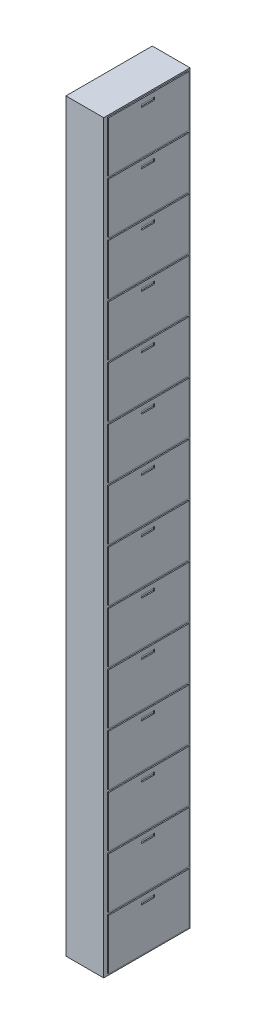
SolidWorks part; units mm, degrees
ref_plane "Front Plane" through (0, 0, 0) normal (0, 0, 1) x (1, 0, 0)
ref_plane "Top Plane" through (0, 0, 0) normal (0, 1, 0) x (1, 0, 0)
ref_plane "Right Plane" through (0, 0, 0) normal (1, 0, 0) x (0, 0, -1)
sketch "Sketch1" plane through (0, 0, 0) normal (0, 0, 1) x (1, 0, 0)
  line L0 (213.062, 4179.9863) -> (-136.938, 4179.9863)
  line L1 (-136.938, 4179.9863) -> (-136.938, -2720.0137)
  line L2 (-136.938, -2720.0137) -> (213.062, -2720.0137)
  line L5 (213.062, -2720.0137) -> (213.062, 4179.9863)
  dimension "D1" = 350
  dimension "D2" = 6900
extrude "Boss-Extrude1" add sketch "Sketch1" along normal blind 800
sketch "Sketch3" plane through (213.062, 0, 0) normal (1, 0, 0) x (0, 0, -1)
  line L0 (0, -2720.0137) -> (0, 4179.9863) construction
  line L1 (-763.6321, -2700.0137) -> (-20, -2700.0137)
  line L2 (-763.6321, -2700.0137) -> (-763.6321, -2230.0137)
  line L3 (-763.6321, -2230.0137) -> (-20, -2230.0137)
  line L4 (-20, -2700.0137) -> (-20, -2230.0137)
  line L5 (-800, -2720.0137) -> (0, -2720.0137) construction
  line L6 (-763.6321, -2208.0137) -> (-20, -2208.0137)
  line L7 (-461.6648, -2274.1108) -> (-340.5919, -2274.1108)
  line L8 (-461.6648, -2274.1108) -> (-461.6648, -2299.9132)
  line L9 (-461.6648, -2299.9132) -> (-340.5919, -2299.9132)
  line L10 (-340.5919, -2274.1108) -> (-340.5919, -2299.9132)
  line L11 (-763.6321, -2208.0137) -> (-763.6321, -1738.0137)
  line L12 (-763.6321, -1738.0137) -> (-20, -1738.0137)
  line L13 (-20, -2208.0137) -> (-20, -1738.0137)
  line L14 (-461.6648, -1782.1108) -> (-340.5919, -1782.1108)
  line L15 (-461.6648, -1807.9132) -> (-340.5919, -1807.9132)
  line L16 (-461.6648, -1782.1108) -> (-461.6648, -1807.9132)
  line L17 (-340.5919, -1782.1108) -> (-340.5919, -1807.9132)
  line L18 (-763.6321, -1716.0137) -> (-20, -1716.0137)
  line L19 (-763.6321, -1716.0137) -> (-763.6321, -1246.0137)
  line L20 (-763.6321, -1246.0137) -> (-20, -1246.0137)
  line L21 (-20, -1716.0137) -> (-20, -1246.0137)
  line L22 (-461.6648, -1290.1108) -> (-340.5919, -1290.1108)
  line L23 (-461.6648, -1315.9132) -> (-340.5919, -1315.9132)
  line L24 (-461.6648, -1290.1108) -> (-461.6648, -1315.9132)
  line L25 (-340.5919, -1290.1108) -> (-340.5919, -1315.9132)
  line L26 (-763.6321, -1224.0137) -> (-20, -1224.0137)
  line L27 (-763.6321, -1224.0137) -> (-763.6321, -754.0137)
  line L28 (-763.6321, -754.0137) -> (-20, -754.0137)
  line L29 (-20, -1224.0137) -> (-20, -754.0137)
  line L30 (-461.6648, -798.1108) -> (-340.5919, -798.1108)
  line L31 (-461.6648, -823.9132) -> (-340.5919, -823.9132)
  line L34 (-461.6648, -798.1108) -> (-461.6648, -823.9132)
  line L35 (-340.5919, -798.1108) -> (-340.5919, -823.9132)
  line L36 (-763.6321, -732.0137) -> (-20, -732.0137)
  line L37 (-763.6321, -732.0137) -> (-763.6321, -262.0137)
  line L38 (-763.6321, -262.0137) -> (-20, -262.0137)
  line L39 (-20, -732.0137) -> (-20, -262.0137)
  line L40 (-461.6648, -306.1108) -> (-340.5919, -306.1108)
  line L41 (-461.6648, -331.9132) -> (-340.5919, -331.9132)
  line L42 (-461.6648, -306.1108) -> (-461.6648, -331.9132)
  line L43 (-340.5919, -306.1108) -> (-340.5919, -331.9132)
  line L44 (-763.6321, -240.0137) -> (-20, -240.0137)
  line L45 (-763.6321, -240.0137) -> (-763.6321, 229.9863)
  line L46 (-763.6321, 229.9863) -> (-20, 229.9863)
  line L47 (-20, -240.0137) -> (-20, 229.9863)
  line L48 (-461.6648, 185.8892) -> (-340.5919, 185.8892)
  line L49 (-461.6648, 160.0868) -> (-340.5919, 160.0868)
  line L50 (-461.6648, 185.8892) -> (-461.6648, 160.0868)
  line L51 (-340.5919, 185.8892) -> (-340.5919, 160.0868)
  line L52 (-763.6321, 251.9863) -> (-20, 251.9863)
  line L53 (-763.6321, 251.9863) -> (-763.6321, 721.9863)
  line L54 (-763.6321, 721.9863) -> (-20, 721.9863)
  line L55 (-20, 251.9863) -> (-20, 721.9863)
  line L56 (-461.6648, 677.8892) -> (-340.5919, 677.8892)
  line L57 (-461.6648, 652.0868) -> (-340.5919, 652.0868)
  line L58 (-461.6648, 677.8892) -> (-461.6648, 652.0868)
  line L59 (-340.5919, 677.8892) -> (-340.5919, 652.0868)
  line L60 (-763.6321, 743.9863) -> (-20, 743.9863)
  line L61 (-763.6321, 743.9863) -> (-763.6321, 1213.9863)
  line L62 (-763.6321, 1213.9863) -> (-20, 1213.9863)
  line L63 (-20, 743.9863) -> (-20, 1213.9863)
  line L64 (-461.6648, 1169.8892) -> (-340.5919, 1169.8892)
  line L65 (-461.6648, 1144.0868) -> (-340.5919, 1144.0868)
  line L66 (-461.6648, 1169.8892) -> (-461.6648, 1144.0868)
  line L67 (-340.5919, 1169.8892) -> (-340.5919, 1144.0868)
  line L68 (-763.6321, 1235.9863) -> (-20, 1235.9863)
  line L69 (-763.6321, 1235.9863) -> (-763.6321, 1705.9863)
  line L70 (-763.6321, 1705.9863) -> (-20, 1705.9863)
  line L71 (-20, 1235.9863) -> (-20, 1705.9863)
  line L72 (-461.6648, 1661.8892) -> (-340.5919, 1661.8892)
  line L73 (-461.6648, 1636.0868) -> (-340.5919, 1636.0868)
  line L74 (-461.6648, 1661.8892) -> (-461.6648, 1636.0868)
  line L75 (-340.5919, 1661.8892) -> (-340.5919, 1636.0868)
  line L76 (-763.6321, 1727.9863) -> (-20, 1727.9863)
  line L77 (-763.6321, 1727.9863) -> (-763.6321, 2197.9863)
  line L78 (-763.6321, 2197.9863) -> (-20, 2197.9863)
  line L79 (-20, 1727.9863) -> (-20, 2197.9863)
  line L80 (-461.6648, 2153.8892) -> (-340.5919, 2153.8892)
  line L81 (-461.6648, 2128.0868) -> (-340.5919, 2128.0868)
  line L82 (-461.6648, 2153.8892) -> (-461.6648, 2128.0868)
  line L83 (-340.5919, 2153.8892) -> (-340.5919, 2128.0868)
  line L84 (-763.6321, 2219.9863) -> (-20, 2219.9863)
  line L85 (-763.6321, 2219.9863) -> (-763.6321, 2689.9863)
  line L86 (-763.6321, 2689.9863) -> (-20, 2689.9863)
  line L87 (-20, 2219.9863) -> (-20, 2689.9863)
  line L88 (-461.6648, 2645.8892) -> (-340.5919, 2645.8892)
  line L89 (-461.6648, 2620.0868) -> (-340.5919, 2620.0868)
  line L90 (-461.6648, 2645.8892) -> (-461.6648, 2620.0868)
  line L91 (-340.5919, 2645.8892) -> (-340.5919, 2620.0868)
  line L92 (-763.6321, 2711.9863) -> (-20, 2711.9863)
  line L93 (-763.6321, 2711.9863) -> (-763.6321, 3181.9863)
  line L94 (-763.6321, 3181.9863) -> (-20, 3181.9863)
  line L95 (-20, 2711.9863) -> (-20, 3181.9863)
  line L96 (-461.6648, 3137.8892) -> (-340.5919, 3137.8892)
  line L97 (-461.6648, 3112.0868) -> (-340.5919, 3112.0868)
  line L98 (-461.6648, 3137.8892) -> (-461.6648, 3112.0868)
  line L99 (-340.5919, 3137.8892) -> (-340.5919, 3112.0868)
  line L100 (-763.6321, 3203.9863) -> (-20, 3203.9863)
  line L101 (-763.6321, 3203.9863) -> (-763.6321, 3673.9863)
  line L102 (-763.6321, 3673.9863) -> (-20, 3673.9863)
  line L103 (-20, 3203.9863) -> (-20, 3673.9863)
  line L104 (-461.6648, 3629.8892) -> (-340.5919, 3629.8892)
  line L105 (-461.6648, 3604.0868) -> (-340.5919, 3604.0868)
  line L106 (-461.6648, 3629.8892) -> (-461.6648, 3604.0868)
  line L107 (-340.5919, 3629.8892) -> (-340.5919, 3604.0868)
  line L108 (-763.6321, 3695.9863) -> (-20, 3695.9863)
  line L109 (-763.6321, 3695.9863) -> (-763.6321, 4165.9863)
  line L110 (-763.6321, 4165.9863) -> (-20, 4165.9863)
  line L111 (-20, 3695.9863) -> (-20, 4165.9863)
  line L112 (-461.6648, 4121.8892) -> (-340.5919, 4121.8892)
  line L113 (-461.6648, 4096.0868) -> (-340.5919, 4096.0868)
  line L114 (-461.6648, 4121.8892) -> (-461.6648, 4096.0868)
  line L115 (-340.5919, 4121.8892) -> (-340.5919, 4096.0868)
  dimension "D1" = 470
  dimension "D2" = 20
  dimension "D3" = 20
  dimension "D4" = 14
extrude "Boss-Extrude3" add sketch "Sketch3" along normal blind 10 contours L1 L4 L3 L2 L7 L10 L9 L8 | L18 L21 L20 L19 L22 L25 L23 L24 | L6 L13 L12 L11 L14 L17 L15 L16 | L26 L29 L28 L27 L30 L35 L31 L34 | L36 L39 L38 L37 L40 L43 L41 L42 | L44 L47 L46 L45 L48 L51 L49 L50 | L52 L55 L54 L53 L56 L59 L57 L58 | L60 L63 L62 L61 L64 L67 L65 L66 | L68 L71 L70 L69 L72 L75 L73 L74 | L76 L79 L78 L77 L80 L83 L81 L82 | L84 L87 L86 L85 L88 L91 L89 L90 | L92 L95 L94 L93 L96 L99 L97 L98 | L100 L103 L102 L101 L104 L107 L105 L106 | L108 L111 L110 L109 L112 L115 L113 L114
